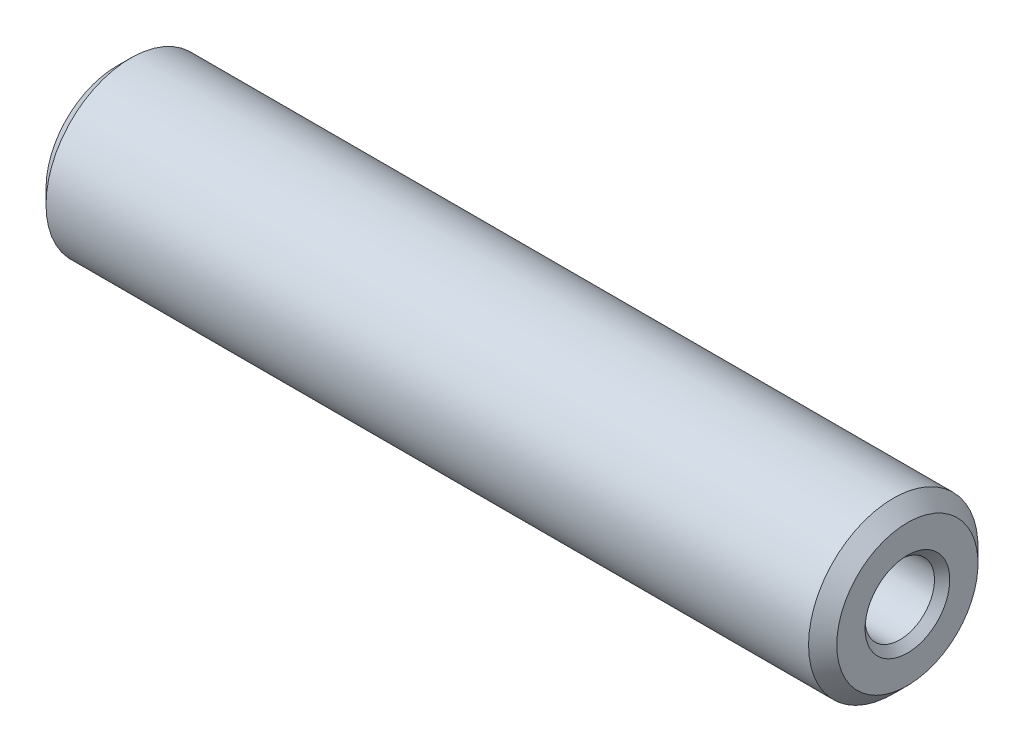
SolidWorks part; units mm, degrees
ref_plane "Front Plane" through (0, 0, 0) normal (0, 0, 1) x (1, 0, 0)
ref_plane "Top Plane" through (0, 0, 0) normal (0, 1, 0) x (1, 0, 0)
ref_plane "Right Plane" through (0, 0, 0) normal (1, 0, 0) x (0, 0, -1)
ref_plane "Plane1" through (0, 0, 0) normal (0, 0, -1) x (-1, 0, 0)
sketch "Sketch1" plane through (0, 0, 0) normal (0, 0, -1) x (-1, 0, 0)
  line L0 (-17.2099, 1.2295) -> (-16.5, 0)
  line L1 (-16.5, 0) -> (-11.5, 0)
  line L2 (-11.5, 0) -> (-10.7901, 1.2295)
  line L3 (-10.7901, 1.2295) -> (-0.2705, 1.2295)
  line L4 (-0.2705, 1.2295) -> (0, 1.5)
  line L5 (0, 1.5) -> (0, 2.5)
  line L6 (0, 2.5) -> (-0.5, 3)
  line L7 (-0.5, 3) -> (-27.5, 3)
  line L8 (-27.5, 3) -> (-28, 2.5)
  line L9 (-28, 2.5) -> (-28, 1.5)
  line L10 (-28, 1.5) -> (-27.7295, 1.2295)
  line L11 (-27.7295, 1.2295) -> (-17.2099, 1.2295)
  line L12 (-28, 0) -> (0, 0) construction
revolve "Revolve1" add sketch "Sketch1" angle 360 about L12
